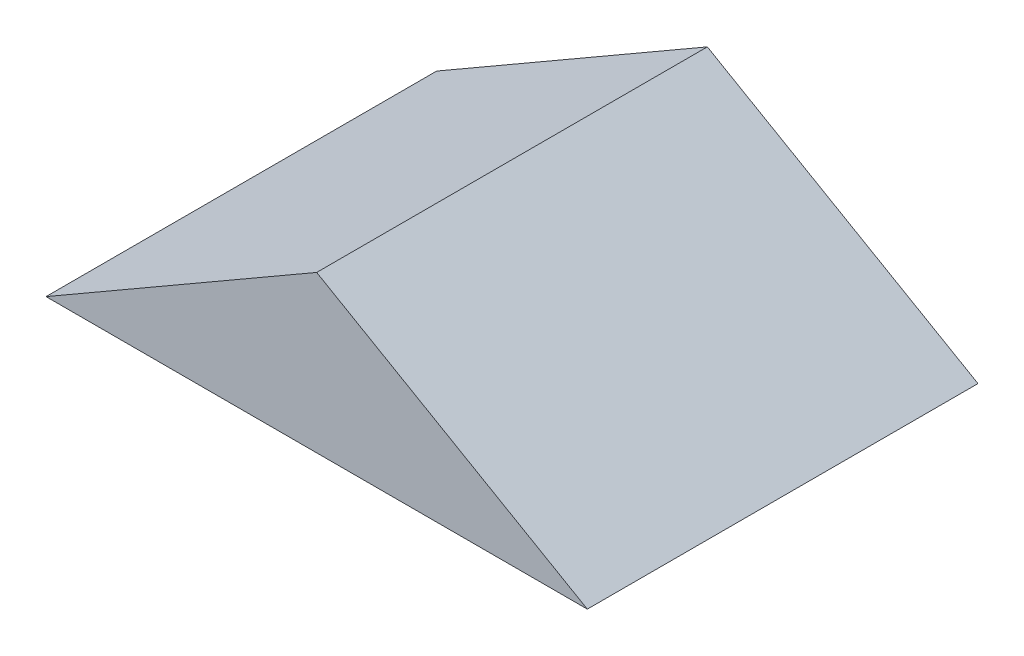
SolidWorks part; units mm, degrees
ref_plane "Front Plane" through (0, 0, 0) normal (0, 0, 1) x (1, 0, 0)
ref_plane "Top Plane" through (0, 0, 0) normal (0, 1, 0) x (1, 0, 0)
ref_plane "Right Plane" through (0, 0, 0) normal (1, 0, 0) x (0, 0, -1)
sketch "Sketch1" plane through (0, 0, 0) normal (0, 0, 1) x (1, 0, 0)
  line L0 (-8.7988, 0) -> (8.7988, 0)
  line L1 (8.7988, 0) -> (0, 5.08)
  line L2 (0, 5.08) -> (-8.7988, 0)
  point P0 (0, 0)
  point P4 (0, 0)
  dimension "D1" = 5.08
  dimension "D2" = 30
extrude "Boss-Extrude1" add sketch "Sketch1" along normal blind 12.7 contours L2 L0 L1
